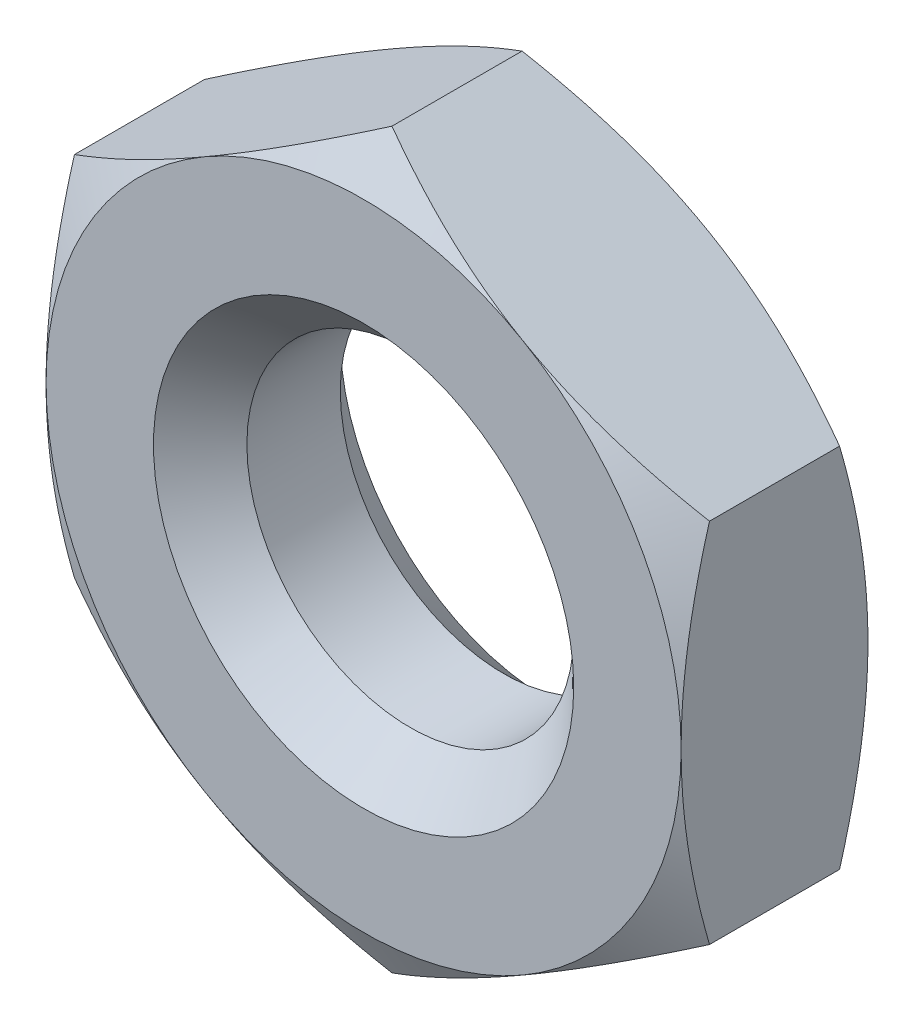
SolidWorks part; units mm, degrees
ref_plane "Спереди" through (0, 0, 0) normal (0, 0, 1) x (1, 0, 0)
ref_plane "Сверху" through (0, 0, 0) normal (0, 1, 0) x (1, 0, 0)
ref_plane "Справа" through (0, 0, 0) normal (1, 0, 0) x (0, 0, -1)
sketch "Эскиз1" plane through (0, 0, 0) normal (0, 0, 1) x (1, 0, 0)
  line L0 (0, -9.815) -> (0, 9.815) construction
  line L1 (8.5, -4.9075) -> (8.5, 4.9075)
  line L2 (8.5, 4.9075) -> (0, 9.815)
  line L3 (0, 9.815) -> (-8.5, 4.9075)
  line L4 (-8.5, 4.9075) -> (-8.5, -4.9075)
  line L5 (-8.5, -4.9075) -> (0, -9.815)
  line L6 (0, -9.815) -> (8.5, -4.9075)
  circle A0 centre (0, 0) radius 8.5 construction
  circle A1 centre (0, 0) radius 4.375
  dimension "D1" = 8.75
  dimension "D2" = 17
extrude "Бобышка-Вытянуть1" add sketch "Эскиз1" along normal blind 5
chamfer "Фаска1" distance 1.25 angle 45 2 edges at (4.375, 0, 5) (4.375, 0, 0)
ref_plane "Плоскость1" through (0, 0, 0) normal (1, 0, 0) x (0, 0, -1)
sketch "Эскиз3" plane through (0, 0, 0) normal (1, 0, 0) x (0, 0, -1)
  line L0 (-0.7592, 9.815) -> (0, 9.815)
  line L1 (0, 9.815) -> (0, 8.5)
  line L2 (0, 8.5) -> (-0.7592, 9.815)
  line L3 (-4.2408, 9.815) -> (-5, 8.5)
  line L4 (-5, 8.5) -> (-5, 9.815)
  line L5 (-5, 9.815) -> (-4.2408, 9.815)
  line L6 (0, 0) -> (-4.7219, 0) construction
  line L8 (0, 8.5) -> (0, -8.5) construction
  line L9 (0, -9.815) -> (0, 9.815) construction
  dimension "D1" = 30
revolve "Вырез-Повернуть1" cut sketch "Эскиз3" angle 360 about L6
